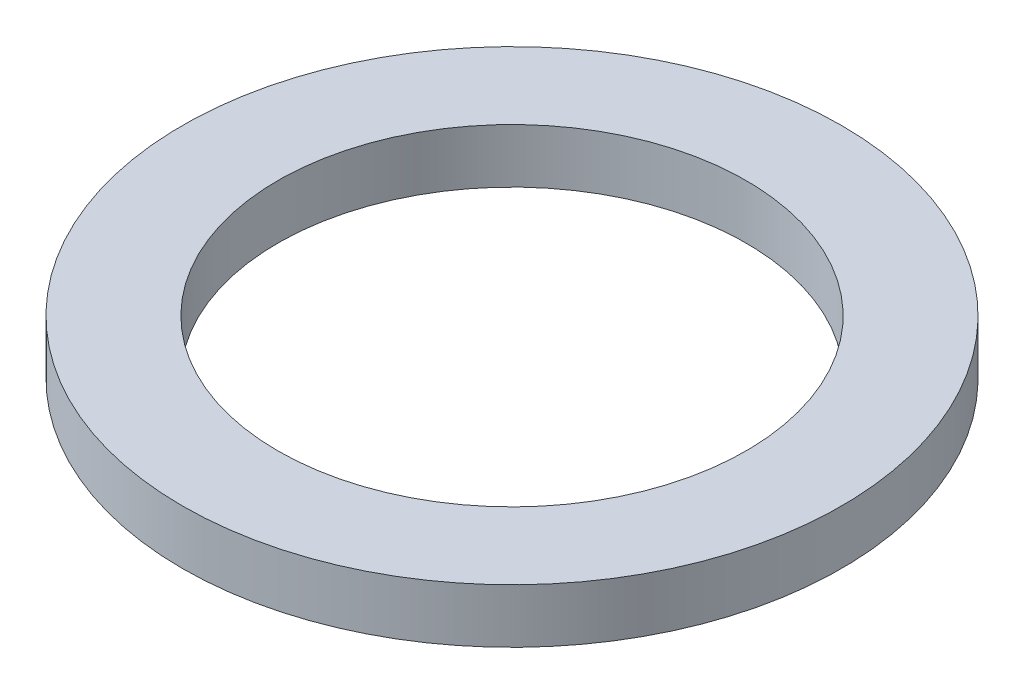
SolidWorks part; units mm, degrees
ref_plane "Front Plane" through (0, 0, 0) normal (0, 0, 1) x (1, 0, 0)
ref_plane "Top Plane" through (0, 0, 0) normal (0, 1, 0) x (1, 0, 0)
ref_plane "Right Plane" through (0, 0, 0) normal (1, 0, 0) x (0, 0, -1)
sketch "Sketch1" plane through (0, 0, 0) normal (0, 1, 0) x (1, 0, 0)
  circle A0 centre (0, 0) radius 3.429
  circle A1 centre (0, 0) radius 5.08 construction
  circle A2 centre (0, 0) radius 4.826
  dimension "D1" = 0.254
  dimension "D2" = 6.858
  dimension "D3" = 10.16
extrude "Boss-Extrude1" add sketch "Sketch1" along normal blind 0.7937
